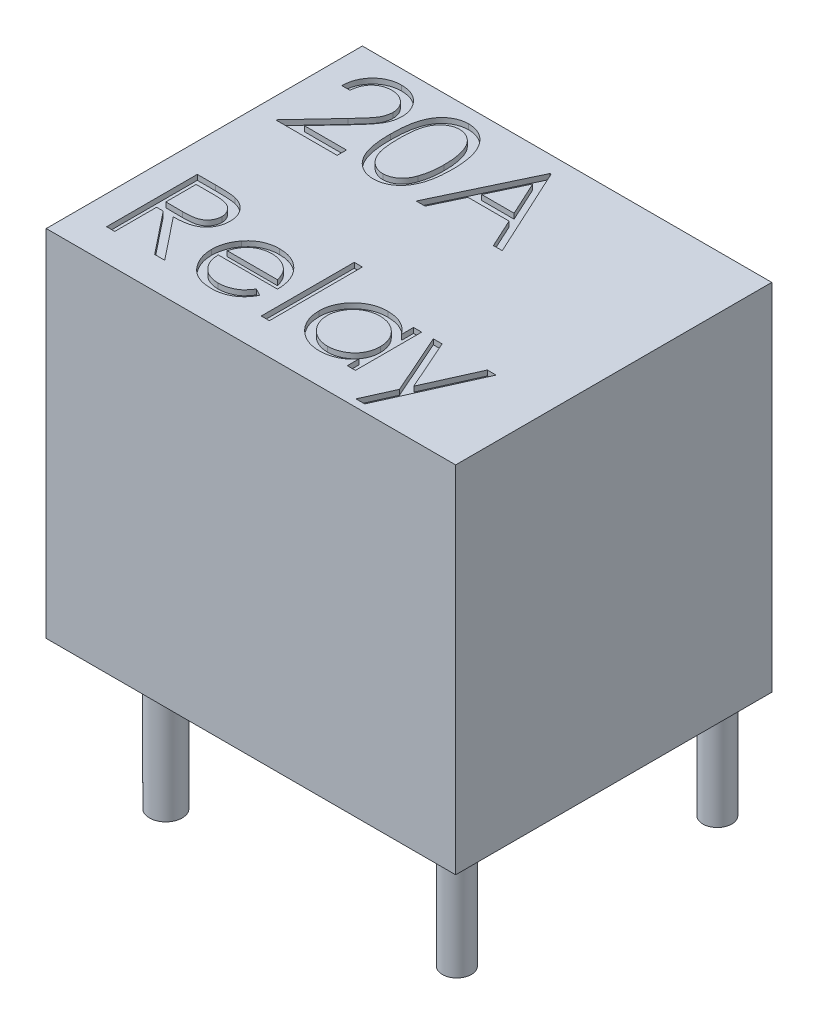
SolidWorks part; units mm, degrees
ref_plane "Front Plane" through (0, 0, 0) normal (0, 0, 1) x (1, 0, 0)
ref_plane "Top Plane" through (0, 0, 0) normal (0, 1, 0) x (1, 0, 0)
ref_plane "Right Plane" through (0, 0, 0) normal (1, 0, 0) x (0, 0, -1)
sketch "Sketch1" plane through (0, 0, 0) normal (0, 1, 0) x (1, 0, 0)
  line L1 (10.1061, -8.7963) -> (-5.6939, -8.7963)
  line L2 (10.1061, -8.7963) -> (10.1061, 3.4037)
  line L3 (10.1061, 3.4037) -> (-5.6939, 3.4037)
  line L4 (-5.6939, -8.7963) -> (-5.6939, 3.4037)
  dimension "D1" = 15.8
  dimension "D2" = 12.2
extrude "Boss-Extrude1" add sketch "Sketch1" along normal blind 13.7
sketch "Sketch2" plane through (0, 13.7, 0) normal (0, 1, 0) x (1, 0, 0)
  text T0 "20A \r\nRelay"
  point P1 (-5.0378, -0.7378)
extrude "Cut-Extrude1" cut sketch "Sketch2" against normal blind 0.2
sketch "Sketch3" plane through (0, 0, 0) normal (0, -1, 0) x (1, 0, 0)
  circle A0 centre (8.9831, 7.625) radius 0.5612
  circle A1 centre (8.9831, -2.427) radius 0.5577
  circle A2 centre (-4.8303, 3.241) radius 0.6727
  circle A3 centre (-1.899, 7.9752) radius 0.6312
  circle A4 centre (-1.7693, -2.3232) radius 0.6163
extrude "Boss-Extrude2" add sketch "Sketch3" along normal blind 4.2
sketch "Sketch4" plane through (0, 0, 0) normal (0, -1, 0) x (1, 0, 0)
  line L1 (-2.1065, 7.0283) -> (-1.5747, 7.0283)
  line L2 (-2.1065, 7.0283) -> (-2.1065, -1.3764)
  line L3 (-2.1065, -1.3764) -> (-1.5747, -1.3764)
  line L4 (-1.5747, 7.0283) -> (-1.5747, -1.3764)
extrude "Boss-Extrude3" add sketch "Sketch4" along normal blind 0.2
